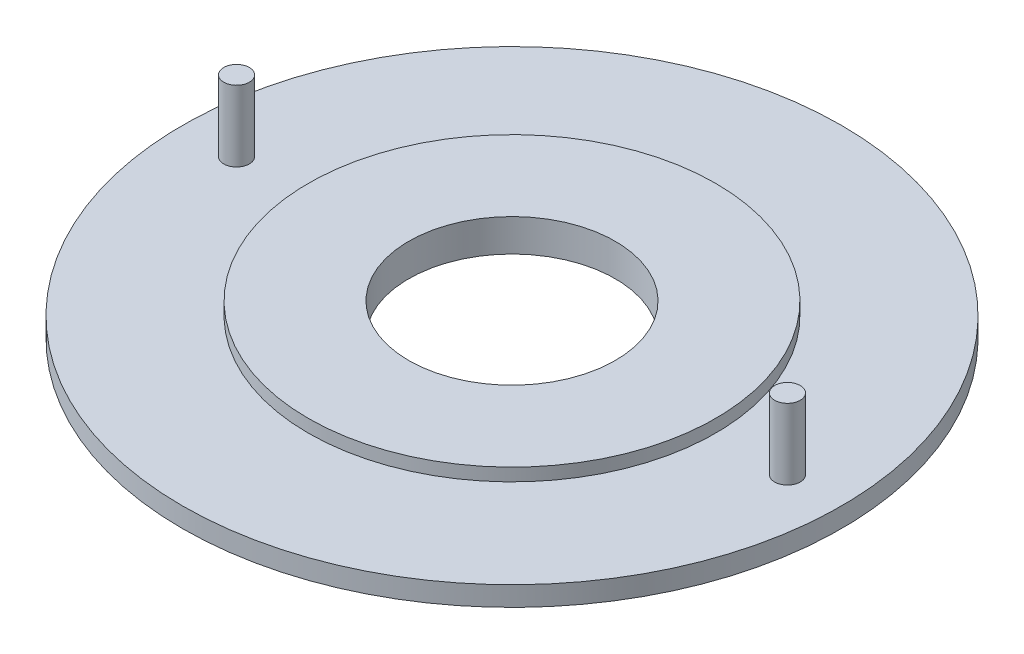
SolidWorks part; units mm, degrees
ref_plane "Спереди" through (0, 0, 0) normal (0, 0, 1) x (1, 0, 0)
ref_plane "Сверху" through (0, 0, 0) normal (0, 1, 0) x (1, 0, 0)
ref_plane "Справа" through (0, 0, 0) normal (1, 0, 0) x (0, 0, -1)
sketch "Эскиз1" plane through (0, 0, 0) normal (0, 1, 0) x (1, 0, 0)
  circle A0 centre (0, 0) radius 16.75
  dimension "D1" = 33.5
extrude "Бобышка-Вытянуть1" add sketch "Эскиз1" along normal blind 1
sketch "Эскиз2" plane through (0, 1, 0) normal (0, 1, 0) x (1, 0, 0)
  circle A0 centre (0, 0) radius 10.35
  dimension "D1" = 20.7
extrude "Бобышка-Вытянуть2" add sketch "Эскиз2" along normal blind 0.65
sketch "Эскиз3" plane through (0, 1.65, 0) normal (0, 1, 0) x (1, 0, 0)
  circle A0 centre (0, 0) radius 5.25
  dimension "D1" = 10.5
extrude "Вырез-Вытянуть1" cut sketch "Эскиз3" against normal through all
sketch "Эскиз4" plane through (0, 1, 0) normal (0, 1, 0) x (1, 0, 0)
  circle A0 centre (14, 0) radius 0.65
  circle A1 centre (14, 0) radius 0.75 construction
  circle A2 centre (-14, 0) radius 0.65
  dimension "D1" = 0.1
extrude "Бобышка-Вытянуть3" add sketch "Эскиз4" along normal offset from surface (3.6 mm away) 2
